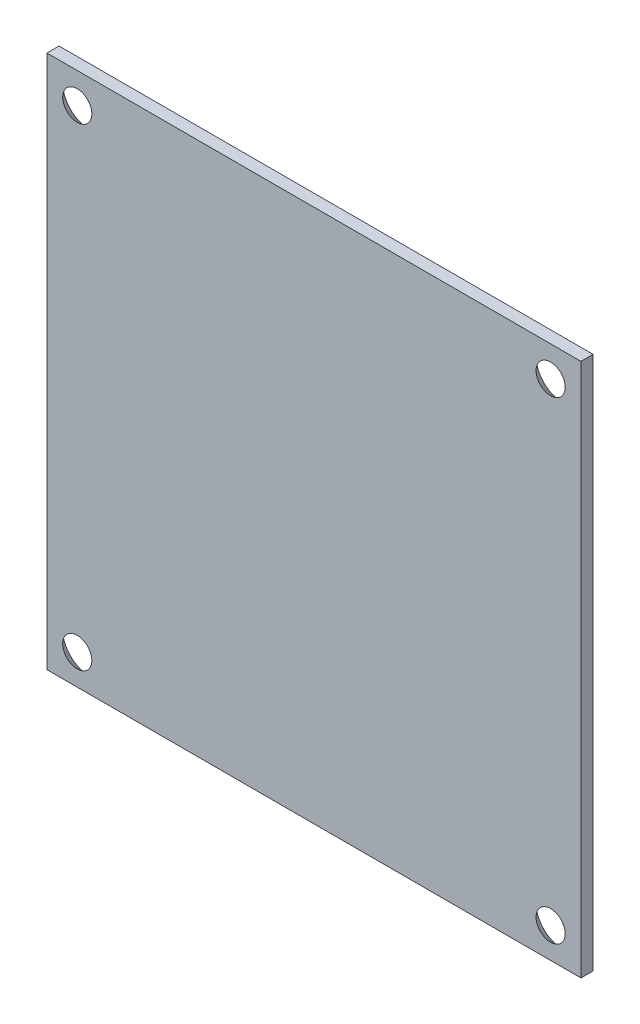
SolidWorks part; units mm, degrees
ref_plane "Plan de face" through (0, 0, 0) normal (1, 0, 0) x (0, 1, 0)
ref_plane "Plan de dessus" through (0, 0, 0) normal (0, 0, 1) x (0, 1, 0)
ref_plane "Plan de droite" through (0, 0, 0) normal (0, 1, 0) x (-1, 0, 0)
sketch "Esquisse1" plane through (0, 0, 0) normal (0, 0, 1) x (0, 1, 0)
  line L1 (-22, -22) -> (22, -22)
  line L2 (-22, -22) -> (-22, 22)
  line L3 (-22, 22) -> (22, 22)
  line L4 (22, -22) -> (22, 22)
  line L5 (-22, -22) -> (22, 22) construction
  line L6 (-22, 22) -> (22, -22) construction
  point P0 (0, 0)
extrude "Boss.-Extru.1" add sketch "Esquisse1" along normal blind 1
hole_wizard "Fraisage pour vis à tête fraisée M21" positions "Esquisse2" profile "Esquisse3" countersink size "M2" standard "Ansi Metric" end condition through all
sketch "Esquisse2" plane through (0, 0, 0) normal (0, 0, -1) x (-1, 0, 0)
  line L0 (-22, 22) -> (22, 22) construction
  line L1 (-22, -22) -> (-22, 22) construction
  line L2 (22, 22) -> (22, -22) construction
  point P0 (-19.5, 19.5)
  point P2 (19.5, 19.5)
  dimension "D2" = 2.5
  dimension "D3" = 2.5
sketch "Esquisse3" plane through (19.5, 19.5, 0) normal (1, 0, 0) x (0, 1, 0)
  line L0 (0, 0) -> (0, 2)
  line L1 (0, 2) -> (1.2, 2)
  line L2 (1.2, 2) -> (1.2, 1)
  line L3 (1.2, 1) -> (2.2, 0)
  line L5 (2.2, 0) -> (0, 0)
  line L6 (-1.2, 1) -> (-2.2, 0) construction
  line L11 (0, -6.35) -> (0, 107.95) construction
  dimension "Diamètre du perçage jusqu'au prochain" = 2.4
  dimension "Profondeur du perçage jusqu'au prochain" = 1
  dimension "Diamètre du fraisage entrant" = 4.4
  dimension "Angle du fraisage entrant" = 90
ref_plane "Plan1" through (0, 0, 0) normal (0, 1, 0) x (1, 0, 0)
mirror "Symétrie2" about plane through (0, 0, 0) normal (0, 1, 0) of "Fraisage pour vis à tête fraisée M21"
equation "\"Plaque_L\" =\"Cavite_L\"+\"Cavite_E\"'longueur plaque"
equation "\"Plaque_H\" = \"Cavite_L\"+\"Cavite_E\"'largeur plaque"
equation "\"Plaque_E\"= 1mm'épaisseur plaque"
equation "\"Trou_R\"= 1.2mm'rayon perforation base"
equation "\"Trou_dx\"= 4mm'distance entre trou sur x"
equation "\"Trou-dy\"= 4mm'distance entre trou sur y"
equation "\"Cavite_largeur\"= 28mm'largeur cavité"
equation "\"Cavite_L\" =\"Cavite_largeur\"+\"Cavite_E\"'longueur cavité"
equation "\"Cavite_E\"= 3mm'épaisseur cavité"
equation "\"Cavite_H\" = 18mm'hauteur cavité"
equation "\"Offset_Z\"= 0mm"
equation "\"Vis_Diam\"= 1.6mm"
equation "\"Offset_Bord\"= \"Cavite_E\" / 2"
equation "\"Vis_Long\"= 5mm"
equation "\"Perc_Passage\"= 1.8mm"
equation "\"Perc_Taraud\"= 1.3mm"
equation "\"Fraisure_Diam\"= 3mm"
equation "\"Fraisure_Prof\"= 1mm"
equation "\"Offset_hauteur_vis1\"= \"Cavite_E\""
equation "\"Offset_hauteur_vis2\"= \"Cavite_H\" - \"Cavite_E\""
equation "\"Perc_Profondeur\"= 8mm"
equation "\"Taraud_Profondeur\"= \"Cavite_E\""
equation "\"H_total\"=113mm'122-2*2"
equation "\"espace_trou\"=22.6mm"
equation "\"D1@Esquisse1\"=\"largeur_plaque_enveloppe\""
equation "\"D1@Boss.-Extru.1\"=\"Plaque_E\""
equation "\"D1@Esquisse2\"=\"Offset_Enveloppe\""
equation "\"D2@Esquisse2\"=\"Offset_Enveloppe\""
equation "\"D3@Esquisse2\"=\"Offset_Enveloppe\""
equation "\"Offset_cavite\" = \"Cavite_E\" / 2"
equation "\"espace_vis\"=22.6mm'"
equation "\"Enveloppe_E\"=5mm"
equation "\"Offset_Enveloppe\" = \"Enveloppe_E\" / 2"
equation "\"Largeur_enveloppe\"=\"Cavite_largeur\"+\"Cavite_E\""
equation "\"Longueur_enveloppe\"=\"Cavite_L\"+\"Enveloppe_E\""
equation "\"N_Plaque\" = 7"
equation "\"N_Cavite\"= 6"
equation "\"Largeur_equerre_enveloppe\"=\"Cavite_L\"+\"Cavite_E\""
equation "\"Longueur_enveloppe_enveloppe\"=\"Cavite_L\"+\"Enveloppe_E\""
equation "\"largeur_plaque_enveloppe\"=\"Longueur_equerre_enveloppe\"+\"Enveloppe_E\""
equation "\"Longueur_equerre_enveloppe\"=\"Cavite_L\"+\"Cavite_E\"+\"Enveloppe_E\""
